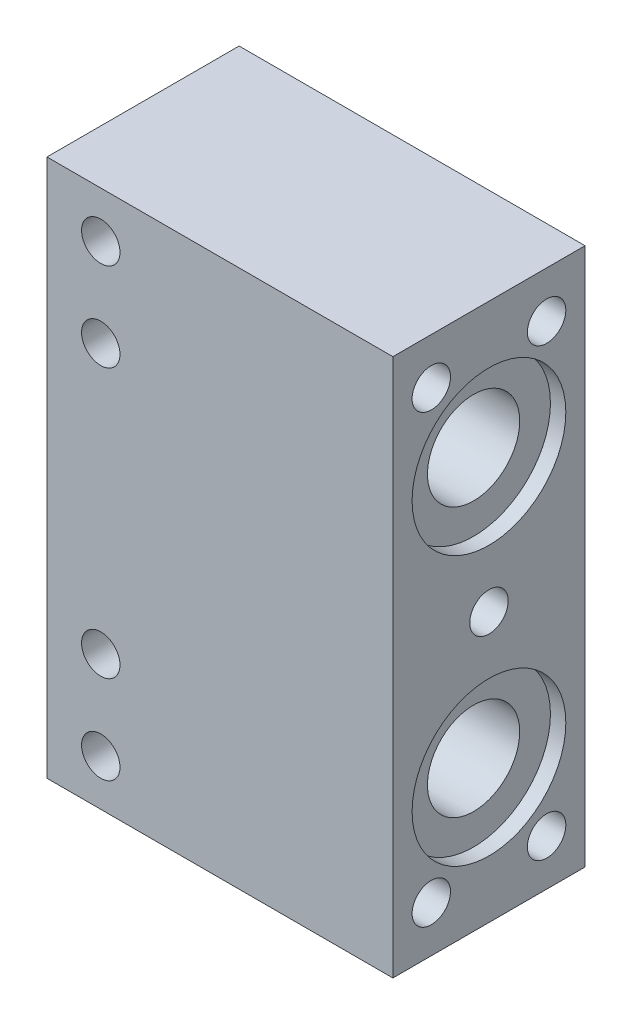
SolidWorks part; units mm, degrees
ref_plane "Front Plane" through (0, 0, 0) normal (0, 0, 1) x (1, 0, 0)
ref_plane "Top Plane" through (0, 0, 0) normal (0, 1, 0) x (1, 0, 0)
ref_plane "Right Plane" through (0, 0, 0) normal (1, 0, 0) x (0, 0, -1)
sketch "Sketch1" plane through (0, 0, 0) normal (0, 1, 0) x (1, 0, 0)
  line L1 (-22.5, 12.5) -> (22.5, 12.5)
  line L2 (-22.5, 12.5) -> (-22.5, -12.5)
  line L3 (-22.5, -12.5) -> (22.5, -12.5)
  line L4 (22.5, 12.5) -> (22.5, -12.5)
  line L5 (-22.5, 12.5) -> (22.5, -12.5) construction
  line L6 (-22.5, -12.5) -> (22.5, 12.5) construction
  point P0 (0, 0)
  dimension "D1" = 25
  dimension "D2" = 45
extrude "Boss-Extrude1" add sketch "Sketch1" along normal blind 70
sketch "Sketch2" plane through (22.5, 0, 0) normal (1, 0, 0) x (0, 0, -1)
  line L0 (-12.5, 70) -> (-12.5, 0) construction
  line L1 (-12.5, 70) -> (12.5, 70) construction
  line L2 (-12.5, 0) -> (12.5, 0) construction
  circle A0 centre (0, 52.5) radius 6
  circle A1 centre (0, 17.5) radius 6
  dimension "D1" = 12.5
  dimension "D3" = 17.5
  dimension "D2" = 17.5
extrude "Cut-Extrude1" cut sketch "Sketch2" against normal blind 70
sketch "Sketch3" plane through (22.5, 0, 0) normal (1, 0, 0) x (0, 0, -1)
  circle A0 centre (0, 17.5) radius 10
  circle A1 centre (0, 52.5) radius 10
extrude "Cut-Extrude2" cut sketch "Sketch3" against normal blind 2
sketch "Sketch4" plane through (-22.5, 0, 0) normal (-1, 0, 0) x (0, 0, 1)
  circle A0 centre (0, 52.5) radius 10
  circle A1 centre (0, 17.5) radius 10
extrude "Cut-Extrude3" cut sketch "Sketch4" against normal blind 2
sketch "Sketch5" plane through (22.5, 0, 0) normal (1, 0, 0) x (0, 0, -1)
  line L0 (-12.5, 70) -> (-12.5, 0) construction
  line L1 (12.5, 70) -> (12.5, 0) construction
  line L2 (-12.5, 70) -> (12.5, 70) construction
  line L3 (-12.5, 0) -> (12.5, 0) construction
  circle A0 centre (7.5, 6) radius 2.5
  circle A1 centre (-7.5, 6) radius 2.5
  circle A2 centre (7.5, 64) radius 2.5
  circle A3 centre (-7.5, 64) radius 2.5
  dimension "D1" = 5
  dimension "D2" = 5
  dimension "D3" = 6
  dimension "D4" = 6
  dimension "D5" = 6
  dimension "D6" = 6
  dimension "D7" = 5
  dimension "D8" = 5
extrude "Cut-Extrude4" cut sketch "Sketch5" against normal blind 15
sketch "Sketch6" plane through (22.5, 0, 0) normal (1, 0, 0) x (0, 0, -1)
  line L0 (-12.5, 70) -> (12.5, 70) construction
  circle A1 centre (0, 35) radius 2.5
  dimension "D1" = 35
extrude "Cut-Extrude5" cut sketch "Sketch6" against normal blind 15
sketch "Sketch7" plane through (0, 0, 12.5) normal (0, 0, 1) x (1, 0, 0)
  line L0 (-22.5, 70) -> (22.5, 70) construction
  line L1 (-22.5, 70) -> (-22.5, 0) construction
  line L2 (-22.5, 0) -> (22.5, 0) construction
  circle A0 centre (-15.5, 52.5) radius 2.5
  circle A1 centre (-15.5, 17.5) radius 2.5
  dimension "D1" = 17.5
  dimension "D3" = 17.5
  dimension "D2" = 7
  dimension "D4" = 7
extrude "Cut-Extrude6" cut sketch "Sketch7" against normal blind 36
sketch "Sketch8" plane through (0, 0, 12.5) normal (0, 0, 1) x (1, 0, 0)
  line L0 (-22.5, 0) -> (22.5, 0) construction
  line L1 (-22.5, 70) -> (22.5, 70) construction
  circle A0 centre (-15.5, 64) radius 2.5
  circle A1 centre (-15.5, 6) radius 2.5
  dimension "D1" = 6
  dimension "D2" = 6
extrude "Cut-Extrude7" cut sketch "Sketch8" against normal blind 38
